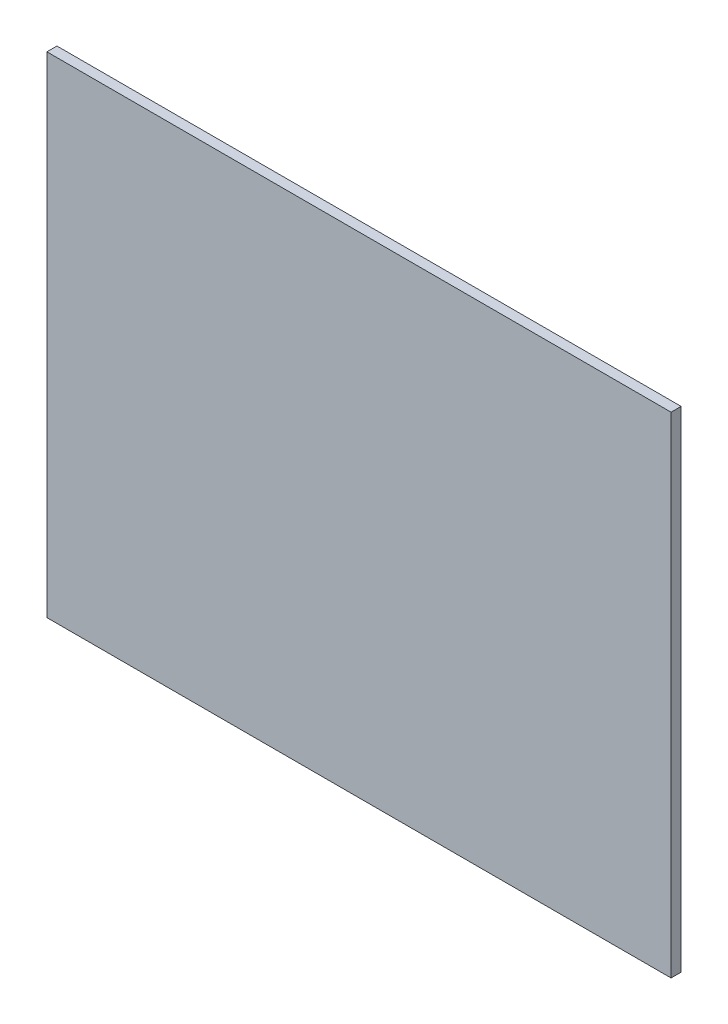
SolidWorks part; units mm, degrees
ref_plane "Front Plane" through (0, 0, 0) normal (0, 0, 1) x (1, 0, 0)
ref_plane "Top Plane" through (0, 0, 0) normal (0, 1, 0) x (1, 0, 0)
ref_plane "Right Plane" through (0, 0, 0) normal (1, 0, 0) x (0, 0, -1)
sketch "Sketch1" plane through (0, 0, 0) normal (0, 0, 1) x (1, 0, 0)
  line L1 (0, 0) -> (155.4, 0)
  line L2 (0, 0) -> (0, 122)
  line L3 (0, 122) -> (155.4, 122)
  line L4 (155.4, 0) -> (155.4, 122)
  dimension "D1" = 155.4
  dimension "D2" = 122
extrude "Boss-Extrude1" add sketch "Sketch1" along normal blind 2.5
